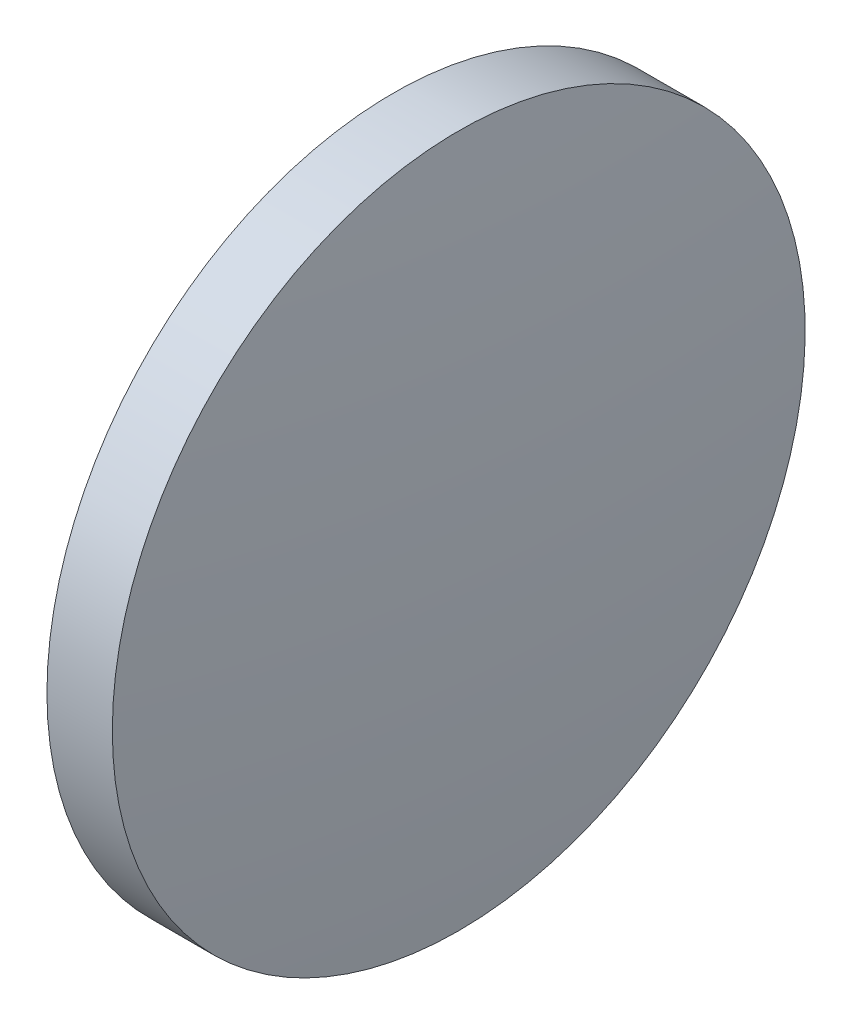
SolidWorks part; units mm, degrees
ref_plane "前视基准面" through (0, 0, 0) normal (0, 0, 1) x (1, 0, 0)
ref_plane "上视基准面" through (0, 0, 0) normal (0, 1, 0) x (1, 0, 0)
ref_plane "右视基准面" through (0, 0, 0) normal (1, 0, 0) x (0, 0, -1)
sketch "草图1" plane through (0, 0, 0) normal (0, 0, 1) x (1, 0, 0)
  line L0 (675.2756, 360.8508) -> (686.0322, 360.8508) construction
  line L1 (679.0009, 360.8508) -> (679.0009, 368.8508)
  line L2 (680.9009, 360.8508) -> (679.0009, 360.8508)
  line L5 (679.0009, 368.8508) -> (680.5109, 368.8508)
  arc A0 (680.9009, 360.8508) -> (680.5109, 368.8508) centre (598.6546, 360.8508) ccw
revolve "旋转1" add sketch "草图1" angle 360 about L0
